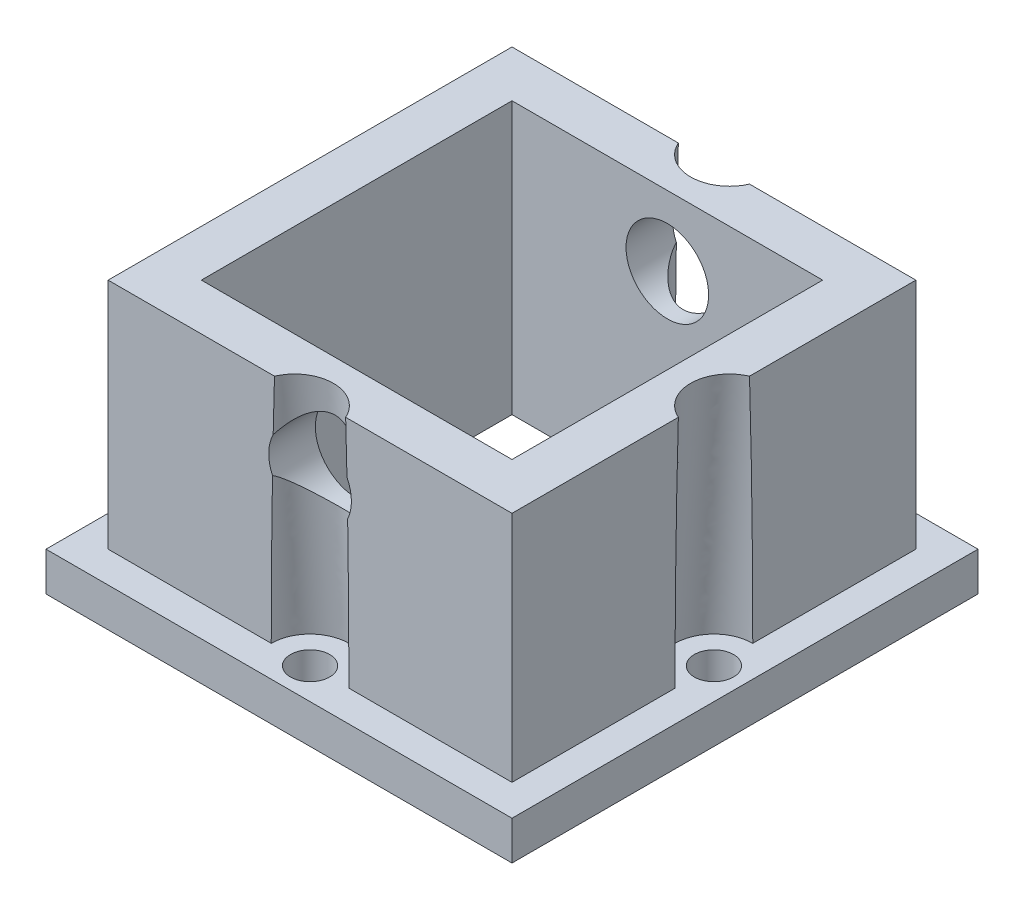
SolidWorks part; units mm, degrees
other "Markup1"
sketch "Sketch8" plane through (19.05, 22.225, -19.05) normal (0.1791, 0.9063, -0.3828) x (-0.9534, 0.0639, -0.2947)
material "PET"
ref_plane "Front Plane" through (0, 0, 0) normal (0, 0, 1) x (1, 0, 0)
ref_plane "Top Plane" through (0, 0, 0) normal (0, 1, 0) x (1, 0, 0)
ref_plane "Right Plane" through (0, 0, 0) normal (1, 0, 0) x (0, 0, -1)
sketch "Sketch1" plane through (0, 0, 0) normal (0, 1, 0) x (1, 0, 0)
  line L1 (-19.05, -19.05) -> (19.05, -19.05)
  line L2 (-19.05, -19.05) -> (-19.05, 19.05)
  line L3 (-19.05, 19.05) -> (19.05, 19.05)
  line L4 (19.05, -19.05) -> (19.05, 19.05)
  line L5 (-19.05, -19.05) -> (19.05, 19.05) construction
  line L6 (-19.05, 19.05) -> (19.05, -19.05) construction
  point P0 (0, 0)
  dimension "D1" = 38.1
  dimension "D2" = 38.1
extrude "Boss-Extrude1" add sketch "Sketch1" along normal blind 3.175
sketch "Sketch2" plane through (0, 3.175, 0) normal (0, 1, 0) x (1, 0, 0)
  line L0 (19.05, 19.05) -> (-19.05, 19.05) construction
  line L1 (-16.51, -16.51) -> (16.51, -16.51)
  line L2 (-16.51, -16.51) -> (-16.51, 16.51)
  line L3 (-16.51, 16.51) -> (16.51, 16.51)
  line L4 (16.51, -16.51) -> (16.51, 16.51)
  line L5 (-16.51, -16.51) -> (16.51, 16.51) construction
  line L6 (-16.51, 16.51) -> (16.51, -16.51) construction
  line L7 (19.05, -19.05) -> (19.05, 19.05) construction
  point P0 (0, 0)
  dimension "D1" = 2.54
  dimension "D2" = 2.54
extrude "Boss-Extrude2" add sketch "Sketch2" along normal blind 19.05
sketch "Sketch3" plane through (0, 22.225, 0) normal (0, 1, 0) x (1, 0, 0)
  line L1 (-12.7, -12.7) -> (12.7, -12.7)
  line L2 (-12.7, -12.7) -> (-12.7, 12.7)
  line L3 (-12.7, 12.7) -> (12.7, 12.7)
  line L4 (12.7, -12.7) -> (12.7, 12.7)
  line L5 (-12.7, -12.7) -> (12.7, 12.7) construction
  line L6 (-12.7, 12.7) -> (12.7, -12.7) construction
  point P0 (0, 0)
  dimension "D1" = 25.4
  dimension "D2" = 25.4
extrude "Cut-Extrude1" cut sketch "Sketch3" against normal through all
ref_plane "Plane1" through (0, 0, 0) normal (0, 0, 1) x (1, 0, 0)
ref_plane "Plane2" through (0, 0, 0) normal (1, 0, 0) x (0, 0, -1)
ref_axis "Axis1" through (0, -1.4288, 0) along (0, 1, 0)
sketch "Sketch4" plane through (0, 3.175, 0) normal (0, 1, 0) x (1, 0, 0)
  line L0 (19.05, -19.05) -> (19.05, 19.05) construction
  circle A0 centre (16.51, 0) radius 1.6002
  dimension "D1" = 3.2004
  dimension "D2" = 2.54
extrude "Cut-Extrude2" cut sketch "Sketch4" against normal through all
pattern_circular "CirPattern1" count 4 over 360 about axis through (0, 0, 0) along (0, 1, 0) skipping 2 of "Cut-Extrude2"
sketch "Sketch6" plane through (0, 0, -16.51) normal (0, 0, -1) x (-1, 0, 0)
  line L0 (-16.51, 12.7) -> (16.51, 12.7) construction
  line L1 (-16.51, 22.225) -> (-16.51, 3.175) construction
  line L2 (16.51, 22.225) -> (16.51, 3.175) construction
  circle A0 centre (0, 16.51) radius 3.3782
  dimension "D1" = 6.7564
  dimension "D2" = 16.51
  dimension "D3" = 3.81
extrude "Cut-Extrude4" cut sketch "Sketch6" against normal through all
sketch "Sketch9" plane through (0, 0, 0) normal (0, 0, 1) x (1, 0, 0)
  line L0 (16.51, 3.175) -> (17.78, 22.225)
  line L1 (16.51, 22.225) -> (16.51, 3.175) construction
  line L3 (-16.51, 22.225) -> (16.51, 22.225) construction
  dimension "D1" = 1.27
  dimension "D2" = 0
sketch "Sketch10" plane through (0, 3.175, 0) normal (0, 1, 0) x (1, 0, 0)
  line L0 (16.51, -1.6002) -> (16.51, 1.6002) construction
  circle A0 centre (16.51, 0) radius 3.175
  dimension "D1" = 6.35
sweep "Cut-Sweep2" cut profiles "Sketch10" path "Sketch9"
pattern_circular "CirPattern3" count 4 over 360 about axis through (0, -1.4288, 0) along (0, 1, 0) skipping 2 of "Cut-Sweep2"
scale "Scale1" [suppressed]
